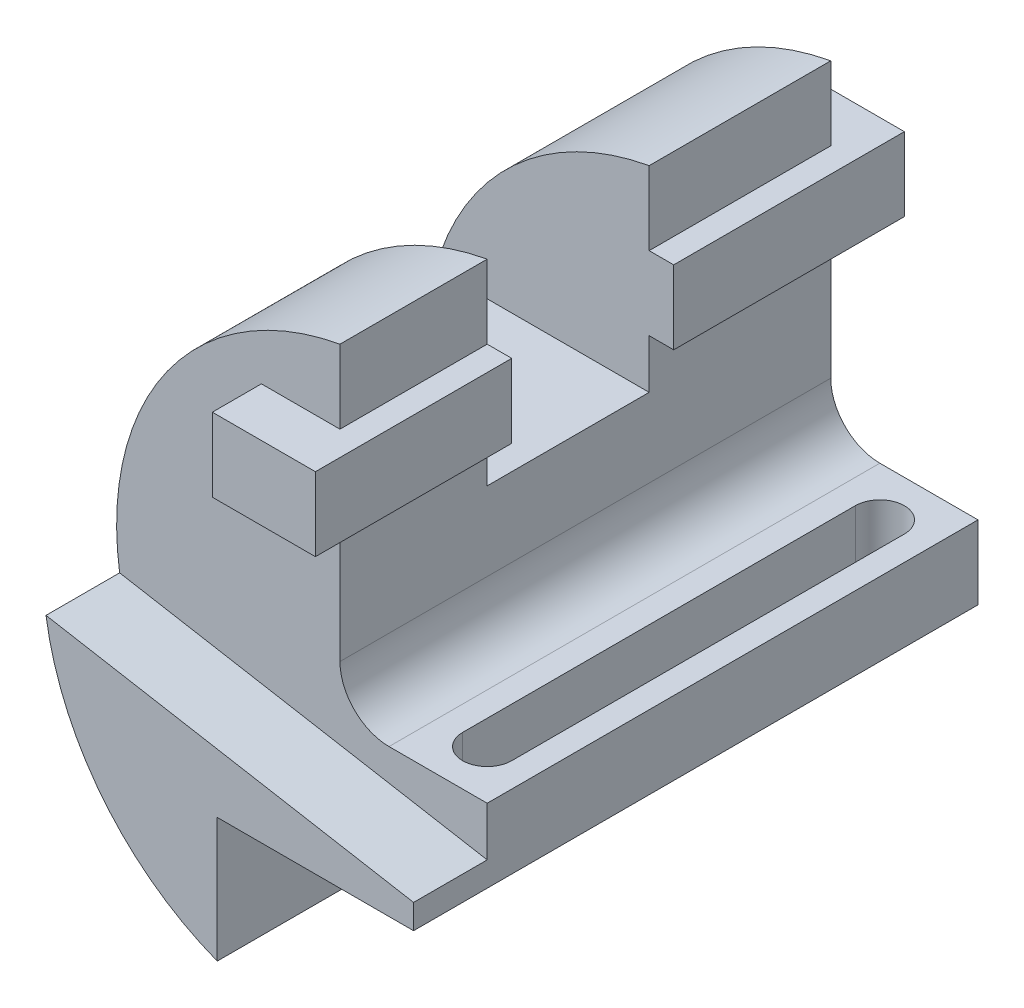
SolidWorks part; units mm, degrees
material "1060 Alloy"
ref_plane "Front Plane" through (0, 0, 0) normal (0, 0, 1) x (1, 0, 0)
ref_plane "Top Plane" through (0, 0, 0) normal (0, 1, 0) x (1, 0, 0)
ref_plane "Right Plane" through (0, 0, 0) normal (1, 0, 0) x (0, 0, -1)
sketch "Sketch1" plane through (0, 0, 0) normal (0, 0, 1) x (1, 0, 0)
  line L0 (0, 0) -> (0, 66)
  line L1 (0, 0) -> (30, 0)
  line L2 (30, 0) -> (30, -15)
  line L3 (30, -15) -> (-10, -15)
  line L4 (-10, -15) -> (-10, -40.3628)
  arc A0 (0, 66) -> (-10, -40.3628) centre (10, 11.4083) ccw
  point P8 (-8.3662, -33.581)
  point P9 (-8.1338, -32.8838)
  dimension "D4" = 55.5
  dimension "D1" = 81
  dimension "D2" = 15
  dimension "D3" = 40
  dimension "D5" = 30
  dimension "D6" = 20
extrude "Boss-Extrude1" add sketch "Sketch1" along normal blind 115
sketch "Sketch2" plane through (0, 0, 115) normal (0, 0, 1) x (1, 0, 0)
  line L0 (30, -10) -> (-44.8904, 3.2052)
  line L1 (30, -15) -> (30, 0) construction
  line L2 (-10, -15) -> (30, -15) construction
  line L7 (30, 0) -> (0, 0) construction
  line L8 (0, 0) -> (0, 66) construction
  line L9 (30, -10) -> (30, 0)
  line L10 (30, 0) -> (0, 0)
  line L11 (0, 0) -> (0, 66)
  arc A0 (0, 66) -> (-10, -40.3628) centre (10, 11.4083) ccw construction
  arc A1 (0, 66) -> (-44.8904, 3.2052) centre (10, 11.4083) ccw
  dimension "D1" = 5
  dimension "D2" = 10
extrude "Cut-Extrude1" cut sketch "Sketch2" against normal blind 15
sketch "Sketch3" plane through (0, 0, 0) normal (0, 0, -1) x (-1, 0, 0)
  line L0 (-5, 51) -> (16, 51)
  line L1 (16, 51) -> (16, 36)
  line L2 (16, 36) -> (-5, 36)
  line L3 (-5, 36) -> (-5, 51)
  line L4 (0, 0) -> (0, 66) construction
  dimension "D1" = 15
  dimension "D2" = 5
  dimension "D3" = 21
  dimension "D4" = 15
extrude "Boss-Extrude2" add sketch "Sketch3" against normal offset from surface 5 and the other way blind 10 up to face at (-2.1532, -16.3726, 115)
sketch "Sketch4" plane through (0, 0, 0) normal (1, 0, 0) x (0, 0, -1)
  line L0 (-70, 66) -> (-37, 66)
  line L1 (-100, 66) -> (0, 66) construction
  line L2 (-37, 66) -> (-37, 26)
  line L3 (-37, 26) -> (-70, 26)
  line L4 (-70, 26) -> (-70, 66)
  dimension "D1" = 33
  dimension "D2" = 30
  dimension "D3" = 40
extrude "Cut-Extrude2" cut sketch "Sketch4" against normal through all both and the other way through all
sketch "Sketch5" plane through (0, 0, 0) normal (0, 1, 0) x (1, 0, 0)
  line L0 (20, -10) -> (20, -90) construction
  line L1 (25, -10) -> (25, -90)
  line L2 (15, -10) -> (15, -90)
  arc A0 (25, -10) -> (15, -10) centre (20, -10) ccw
  arc A1 (15, -90) -> (25, -90) centre (20, -90) ccw
  point P2 (20, -50)
  dimension "D1" = 80
  dimension "D2" = 10
  dimension "D3" = 10
  dimension "D4" = 10
  dimension "D5" = 10
extrude "Cut-Extrude3" cut sketch "Sketch5" against normal through all both
fillet "Fillet1" radius 10 1 edges at (0, 0, 50)
